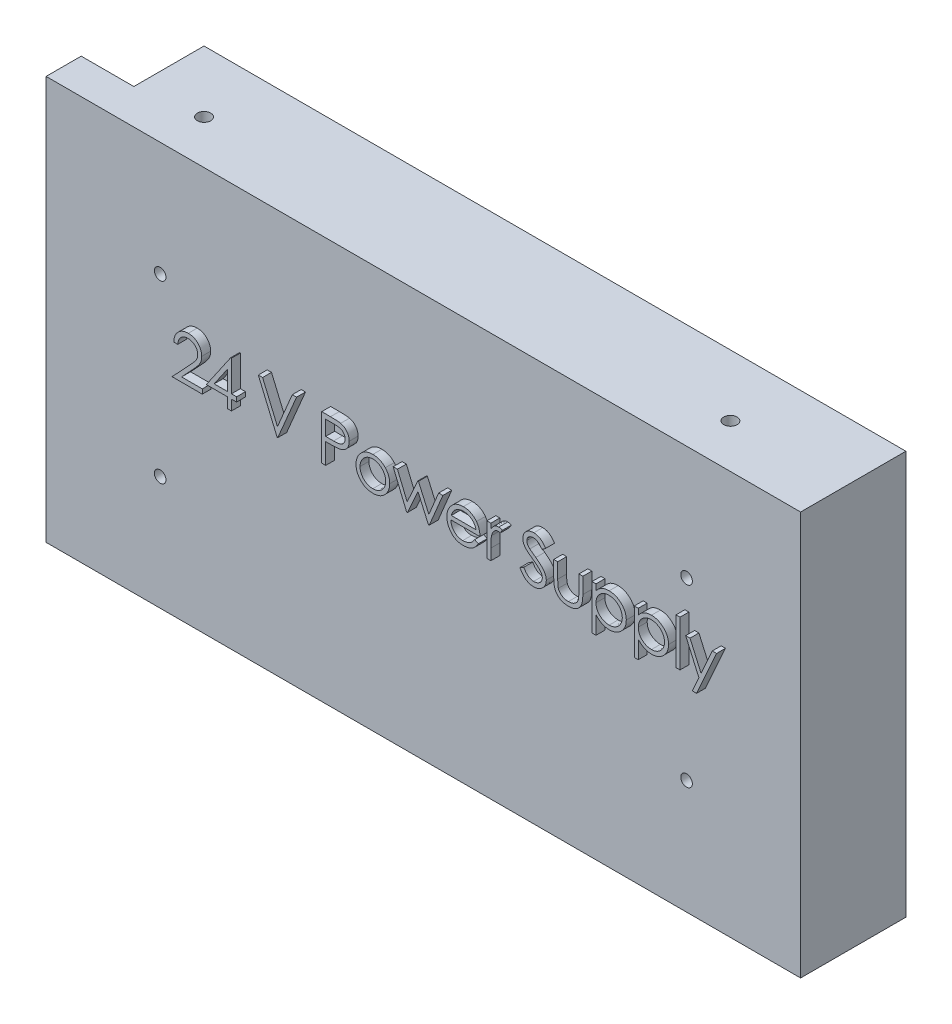
SolidWorks part; units mm, degrees
ref_plane "Front Plane" through (0, 0, 0) normal (0, 0, 1) x (1, 0, 0)
ref_plane "Top Plane" through (0, 0, 0) normal (0, 1, 0) x (1, 0, 0)
ref_plane "Right Plane" through (0, 0, 0) normal (1, 0, 0) x (0, 0, -1)
sketch "Sketch1" plane through (0, 0, 0) normal (0, 0, 1) x (1, 0, 0)
  line L1 (100, -57.5) -> (-100, -57.5)
  line L2 (100, -57.5) -> (100, 57.5)
  line L3 (100, 57.5) -> (-100, 57.5)
  line L4 (-100, -57.5) -> (-100, 57.5)
  line L5 (100, -57.5) -> (-100, 57.5) construction
  line L6 (100, 57.5) -> (-100, -57.5) construction
  point P0 (0, 0)
  dimension "D1" = 200
  dimension "D2" = 115
extrude "Boss-Extrude1" add sketch "Sketch1" along normal blind 30
sketch "Sketch2" plane through (0, 0, 30) normal (0, 0, 1) x (1, 0, 0)
  text T0 "24 V Power Supply" font "Century Gothic" height in points 48
extrude "Boss-Extrude2" add sketch "Sketch2" along normal blind 2.54
sketch "Sketch3" plane through (-100, 0, 0) normal (-1, 0, 0) x (0, 0, 1)
  line L0 (30, 57.5) -> (0, 57.5) construction
  line L1 (30, -57.5) -> (20, -57.5)
  line L2 (30, -57.5) -> (30, 57.5)
  line L3 (30, 57.5) -> (20, 57.5)
  line L4 (20, -57.5) -> (20, 57.5)
  dimension "D1" = 10
extrude "Boss-Extrude3" add sketch "Sketch3" along normal blind 15
sketch "Sketch4" plane through (0, -57.5, 0) normal (0, -1, 0) x (1, 0, 0)
  line L0 (-115, 30) -> (100, 30) construction
  line L1 (-82.5, 17.5) -> (67.5, 17.5) construction
  line L3 (-115, 20) -> (-115, 30) construction
  circle A0 centre (-82.5, 17.5) radius 1.905
  circle A3 centre (67.5, 17.5) radius 1.905
  dimension "D1" = 3.81
  dimension "D2" = 150
  dimension "D3" = 32.5
  dimension "D4" = 12.5
extrude "Cut-Extrude1" cut sketch "Sketch4" against normal through all
hole_wizard "Tap Drill for M4x0.7 Tap1" positions "Sketch6" profile "Sketch7" hole size "M4x0.7" standard "ANSI Metric"
sketch "Sketch6" plane through (0, 0, 30) normal (0, 0, -1) x (-1, 0, 0)
  line L0 (-100, 57.5) -> (100, 57.5) construction
  line L1 (115, 57.5) -> (115, -57.5) construction
  point P0 (-67.5, 25)
  point P2 (82.5, 25)
  point P4 (82.5, -25)
  point P6 (-67.5, -25)
  dimension "D1" = 32.5
  dimension "D2" = 50
  dimension "D3" = 150
  dimension "D4" = 32.5
sketch "Sketch7" plane through (67.5, 25, 30) normal (1, 0, 0) x (0, -1, 0)
  line L0 (0, 0) -> (0, 5.9914)
  line L1 (0, 5.9914) -> (1.65, 5)
  line L2 (1.65, 5) -> (1.65, 0)
  line L5 (1.65, 0) -> (0, 0)
  line L10 (0, 5.9914) -> (-1.65, 5) construction
  line L11 (0, -6.35) -> (0, 107.95) construction
  dimension "Hole Dia." = 3.3
  dimension "Hole Depth" = 5
  dimension "Drill Angle" = 118
sketch "Sketch8" plane through (0, 0, 0) normal (0, 0, -1) x (-1, 0, 0)
  text T0 "FAN SIDE" font "Century Gothic" height 10
extrude "Boss-Extrude4" add sketch "Sketch8" along normal blind 1
